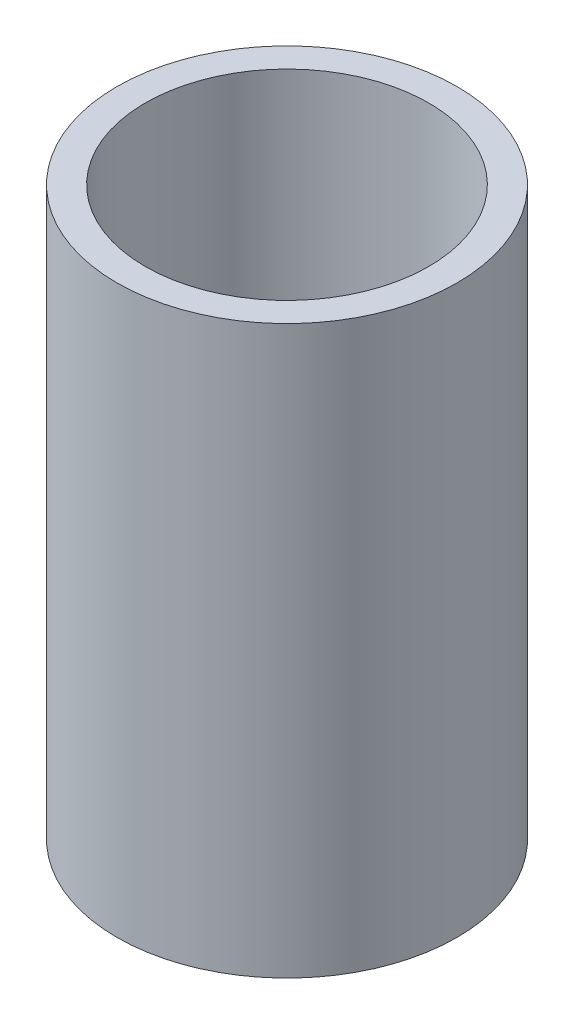
SolidWorks part; units mm, degrees
material "Aluminum Bronze"
ref_plane "Front Plane" through (0, 0, 0) normal (0, 0, 1) x (1, 0, 0)
ref_plane "Top Plane" through (0, 0, 0) normal (0, 1, 0) x (1, 0, 0)
ref_plane "Right Plane" through (0, 0, 0) normal (1, 0, 0) x (0, 0, -1)
sketch "Sketch1" plane through (0, 0, 0) normal (0, 1, 0) x (1, 0, 0)
  circle A0 centre (0, 0) radius 3.9688
  circle A1 centre (0, 0) radius 4.7625
  dimension "D1" = 7.9375
  dimension "D2" = 9.525
extrude "Boss-Extrude1" add sketch "Sketch1" along normal blind 15.875
